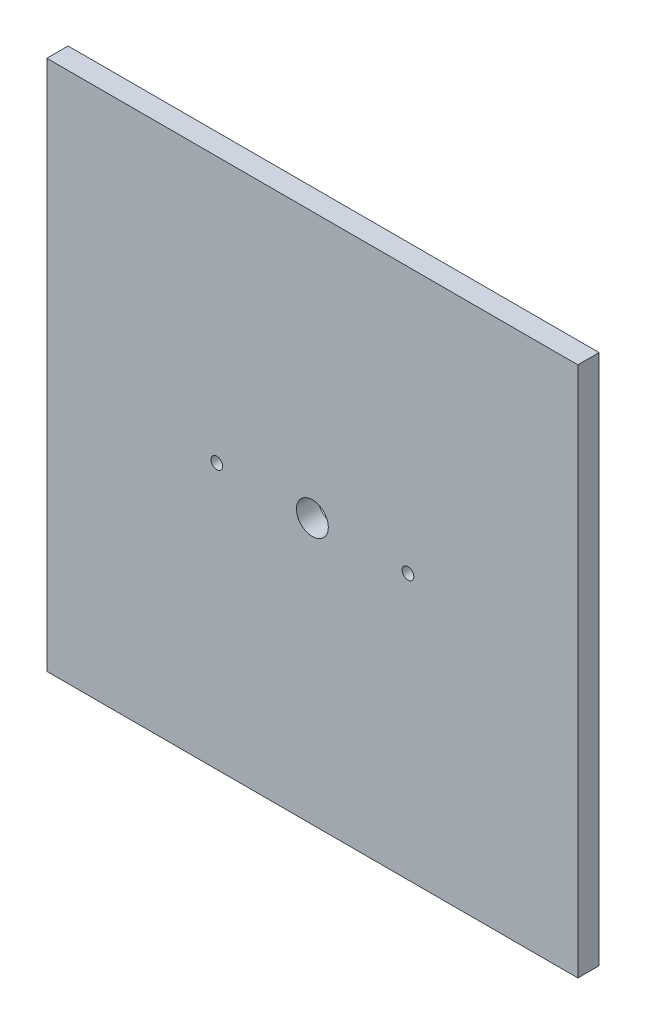
SolidWorks part; units mm, degrees
ref_plane "Ebene vorne" through (0, 0, 0) normal (0, 0, 1) x (1, 0, 0)
ref_plane "Ebene oben" through (0, 0, 0) normal (0, 1, 0) x (1, 0, 0)
ref_plane "Ebene rechts" through (0, 0, 0) normal (1, 0, 0) x (0, 0, -1)
sketch "Skizze1" plane through (0, 0, 0) normal (0, 0, 1) x (1, 0, 0)
  line L1 (125, -125) -> (-125, -125)
  line L2 (125, -125) -> (125, 125)
  line L3 (125, 125) -> (-125, 125)
  line L4 (-125, -125) -> (-125, 125)
  line L5 (125, -125) -> (-125, 125) construction
  line L6 (125, 125) -> (-125, -125) construction
  point P0 (0, 0)
  dimension "D1" = 250
  dimension "D2" = 250
extrude "Aufsatz-Linear austragen1" add sketch "Skizze1" along normal blind 10
hole_wizard "Ø5.5 (5.5) Durchmesser Bohrung1" positions "Skizze2" profile "Skizze3" hole size "Ø5.5" standard "ISO" end condition through all
sketch "Skizze2" plane through (0, 0, 10) normal (0, 0, 1) x (1, 0, 0)
  point P0 (45, 0)
  point P2 (-45, 0)
  dimension "D1" = 45
  dimension "D2" = 45
sketch "Skizze3" plane through (45, 0, 10) normal (1, 0, 0) x (0, -1, 0)
  line L0 (0, 0) -> (0, 10)
  line L1 (0, 10) -> (2.75, 10)
  line L2 (2.75, 10) -> (2.75, 0)
  line L5 (2.75, 0) -> (0, 0)
  line L11 (0, -6.35) -> (0, 107.95) construction
  dimension "Bohrerdurchmesser" = 5.5
  dimension "Bohrungstiefe" = 10
hole_wizard "Ø15.0 (15) Durchmesser Bohrung1" positions "Skizze4" profile "Skizze5" hole size "Ø15.0" standard "ISO" end condition through all
sketch "Skizze4" plane through (0, 0, 10) normal (0, 0, 1) x (1, 0, 0)
  point P0 (0, 0)
sketch "Skizze5" plane through (0, 0, 10) normal (1, 0, 0) x (0, -1, 0)
  line L0 (0, 0) -> (0, 10)
  line L1 (0, 10) -> (7.5, 10)
  line L2 (7.5, 10) -> (7.5, 0)
  line L5 (7.5, 0) -> (0, 0)
  line L11 (0, -6.35) -> (0, 107.95) construction
  dimension "Bohrerdurchmesser" = 15
  dimension "Bohrungstiefe" = 10
